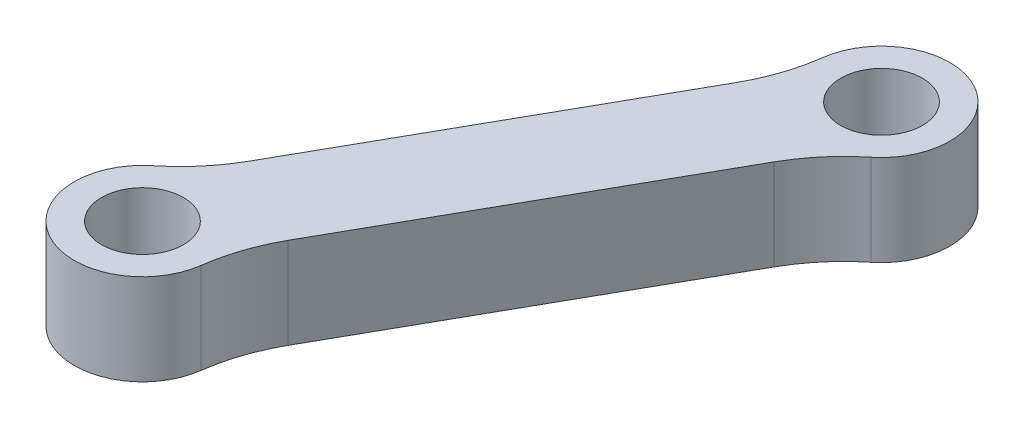
SolidWorks part; units mm, degrees
ref_plane "Front Plane" through (0, 0, 0) normal (0, 0, 1) x (1, 0, 0)
ref_plane "Top Plane" through (0, 0, 0) normal (0, 1, 0) x (1, 0, 0)
ref_plane "Right Plane" through (0, 0, 0) normal (1, 0, 0) x (0, 0, -1)
ref_plane "Plane1" through (0, -63, 0) normal (0, -1, 0) x (1, 0, 0)
sketch "Sketch1" plane through (0, -63, 0) normal (0, -1, 0) x (1, 0, 0)
  line L0 (8.1819, -16.6057) -> (17.8022, -33.6912)
  line L1 (22.6258, -30.9751) -> (13.0056, -13.8897)
  arc A0 (17.8022, -33.6912) -> (19.0008, -37.2757) centre (9.0885, -38.5975) cw
  arc A1 (19.0008, -37.2757) -> (25.0692, -33.8588) centre (22.7179, -36.78) ccw
  arc A2 (25.0692, -33.8588) -> (22.6258, -30.9751) centre (31.3394, -26.0688) cw
  arc A3 (13.0056, -13.8897) -> (11.8069, -10.3051) centre (21.7192, -8.9833) cw
  arc A4 (11.8069, -10.3051) -> (5.7385, -13.7221) centre (8.0898, -10.8008) ccw
  arc A5 (5.7385, -13.7221) -> (8.1819, -16.6057) centre (-0.5317, -21.5121) cw
  circle A6 centre (22.7179, -36.78) radius 2.25
  circle A7 centre (8.0898, -10.8008) radius 2.25
  dimension "D1" = 3.75
  dimension "D2" = 3.75
  dimension "D3" = 4.5
  dimension "D4" = 4.5
extrude "Boss-Extrude1" add sketch "Sketch1" against normal blind 5
